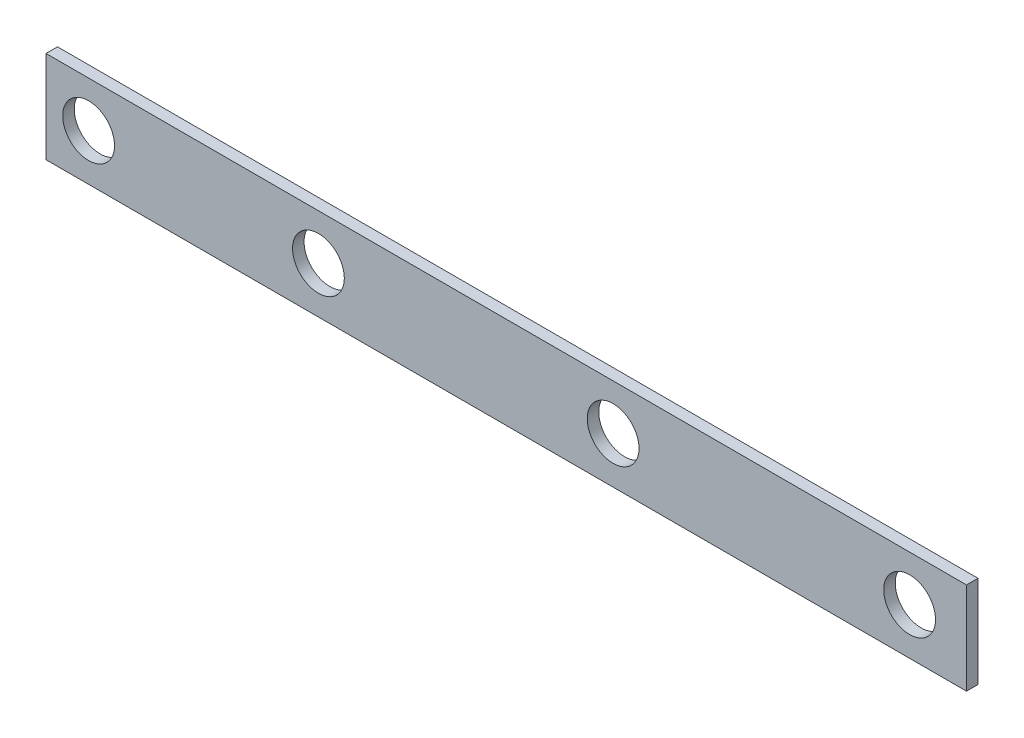
SolidWorks part; units mm, degrees
ref_plane "Front Plane" through (0, 0, 0) normal (0, 0, 1) x (1, 0, 0)
ref_plane "Top Plane" through (0, 0, 0) normal (0, 1, 0) x (1, 0, 0)
ref_plane "Right Plane" through (0, 0, 0) normal (1, 0, 0) x (0, 0, -1)
sketch "Sketch1" plane through (0, 0, 0) normal (0, 0, 1) x (1, 0, 0)
  line L1 (-296.6528, 143.2943) -> (211.3472, 143.2943)
  line L2 (-296.6528, 143.2943) -> (-296.6528, 92.4943)
  line L3 (-296.6528, 92.4943) -> (211.3472, 92.4943)
  line L4 (211.3472, 143.2943) -> (211.3472, 92.4943)
  dimension "D1" = 508
  dimension "D2" = 50.8
extrude "Boss-Extrude1" add sketch "Sketch1" along normal blind 6.35
sketch "Sketch2" plane through (0, 0, 6.35) normal (0, 0, 1) x (1, 0, 0)
  circle A0 centre (-273.1316, 118.1456) radius 14.2875
  circle A1 centre (179.9612, 118.1456) radius 14.2875
  circle A2 centre (-146.307, 118.1456) radius 14.2875
  circle A3 centre (16.3307, 118.1456) radius 14.2875
  dimension "D1" = 28.575
  dimension "D2" = 28.575
  dimension "D3" = 28.575
  dimension "D4" = 28.575
extrude "Cut-Extrude1" cut sketch "Sketch2" against normal blind 6.35
